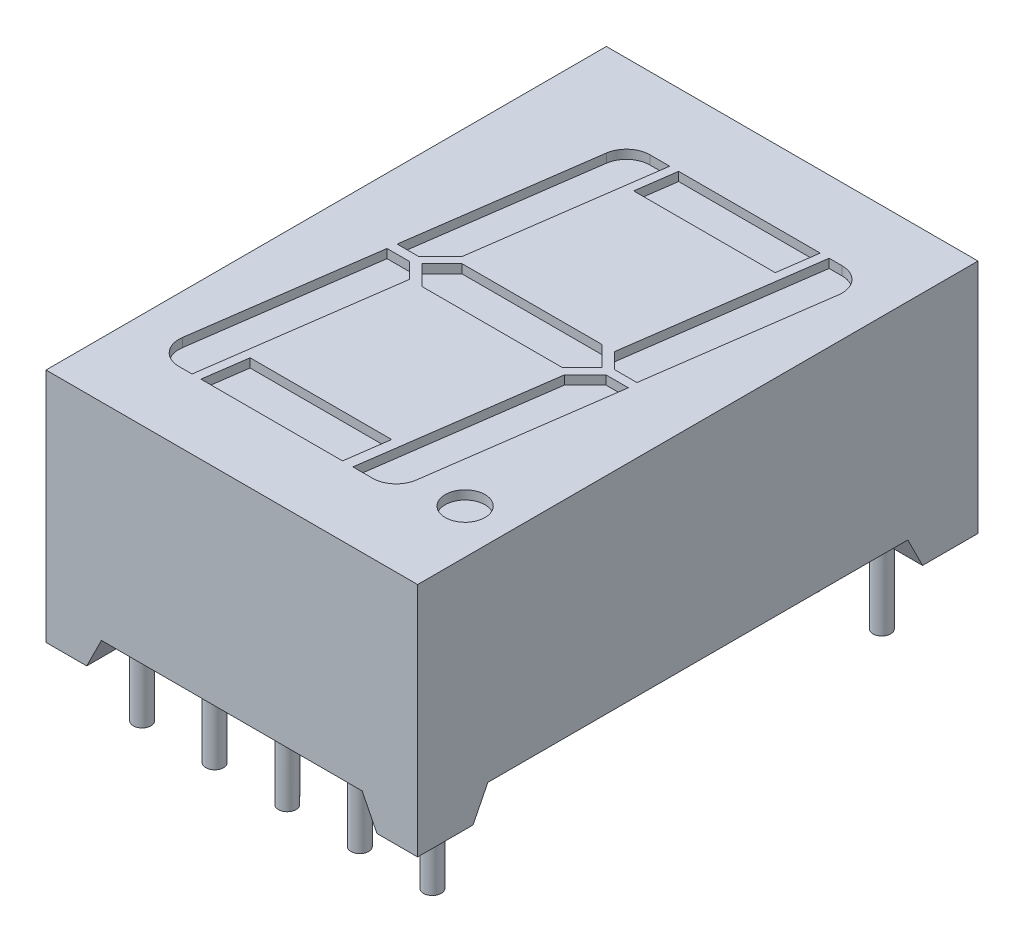
SolidWorks part; units mm, degrees
ref_plane "Front Plane" through (0, 0, 0) normal (0, 0, 1) x (1, 0, 0)
ref_plane "Top Plane" through (0, 0, 0) normal (0, 1, 0) x (1, 0, 0)
ref_plane "Right Plane" through (0, 0, 0) normal (1, 0, 0) x (0, 0, -1)
sketch "Sketch1" plane through (0, 0, 0) normal (0, 1, 0) x (1, 0, 0)
  line L0 (0, 5.3848) -> (0, -5.1523) construction
  line L1 (-6.3, 9.5) -> (6.3, 9.5)
  line L2 (-6.3, 9.5) -> (-6.3, -9.5)
  line L3 (-6.3, -9.5) -> (6.3, -9.5)
  line L4 (6.3, 9.5) -> (6.3, -9.5)
  line L5 (-4.2747, 0) -> (4.8609, 0) construction
  dimension "D1" = 19
  dimension "D2" = 12.6
extrude "Boss-Extrude1" add sketch "Sketch1" along normal blind 8
sketch "Sketch2" plane through (0, 0, 9.5) normal (0, 0, 1) x (1, 0, 0)
  line L0 (-4.92, 0) -> (4.92, 0)
  line L1 (-6.3, 0) -> (6.3, 0) construction
  line L2 (-4.92, 0) -> (-4.42, 1)
  line L3 (-4.42, 1) -> (4.42, 1)
  line L4 (4.42, 1) -> (4.92, 0)
  line L5 (0, 1) -> (0, 0.6203) construction
  line L6 (0, 0) -> (0, -0.1893) construction
  line L7 (0, -0.247) -> (0, 0.4162) construction
  dimension "D1" = 9.84
  dimension "D2" = 8.84
  dimension "D3" = 1
extrude "Cut-Extrude1" cut sketch "Sketch2" against normal through all
sketch "Sketch3" plane through (-6.3, 0, 0) normal (-1, 0, 0) x (0, 0, 1)
  line L0 (-7.62, 0) -> (7.62, 0)
  line L1 (-9.5, 0) -> (9.5, 0) construction
  line L2 (7.62, 0) -> (7.12, 1)
  line L3 (7.12, 1) -> (-7.12, 1)
  line L4 (-7.12, 1) -> (-7.62, 0)
  line L5 (0, 1) -> (0, 0.9495) construction
  line L6 (0, 0) -> (0, 0.4929) construction
  line L7 (0, 0) -> (0, 0.7864) construction
  dimension "D1" = 15.24
  dimension "D2" = 14.24
  dimension "D3" = 1
extrude "Cut-Extrude2" cut sketch "Sketch3" against normal through all
sketch "Sketch4" plane through (0, 8, 0) normal (0, 1, 0) x (1, 0, 0)
  line L0 (0, -8.8185) -> (0, 8.5813) construction
  line L1 (-5.8543, 0) -> (5.7357, 0) construction
  line L2 (0, 0) -> (1.1376, 8.0943) construction
  line L3 (0.9919, 7.0578) -> (0.804, 5.7209) construction
  line L4 (-1.4081, 7.0578) -> (3.3919, 7.0578)
  line L5 (-1.4081, 7.0578) -> (-1.596, 5.7209)
  line L6 (-1.596, 5.7209) -> (3.204, 5.7209)
  line L7 (3.3919, 7.0578) -> (3.204, 5.7209)
  line L8 (-3.1985, -5.6817) -> (1.6015, -5.6817)
  line L9 (-3.1985, -5.6817) -> (-3.4038, -7.1422)
  line L10 (-3.4038, -7.1422) -> (1.3962, -7.1422)
  line L11 (1.6015, -5.6817) -> (1.3962, -7.1422)
  line L12 (-0.7985, -5.6817) -> (-1.0038, -7.1422) construction
  line L13 (-3.0485, 0) -> (-2.3735, 0.675)
  line L14 (-2.3735, 0.675) -> (2.3735, 0.675)
  line L15 (2.3735, 0.675) -> (3.0485, 0)
  line L16 (3.0485, 0) -> (2.3735, -0.675)
  line L17 (2.3735, -0.675) -> (-2.3735, -0.675)
  line L18 (-2.3735, -0.675) -> (-3.0485, 0)
  line L19 (0, 0.675) -> (0, -0.675) construction
  line L20 (3.6949, 7.0578) -> (2.7978, 0.675)
  line L21 (2.7978, 0.675) -> (3.3228, 0.15)
  line L22 (3.3228, 0.15) -> (4.0873, 0.15)
  line L23 (4.0873, 0.15) -> (4.93, 6.1465)
  line L24 (4.1378, 7.0578) -> (3.6949, 7.0578)
  line L25 (3.3392, -0.15) -> (4.0942, -0.15)
  line L26 (4.0942, -0.15) -> (3.2083, -6.4535)
  line L27 (2.4161, -7.1422) -> (1.7483, -7.1422)
  line L28 (1.7483, -7.1422) -> (2.6315, -0.8577)
  line L29 (2.6315, -0.8577) -> (3.3392, -0.15)
  line L30 (-1.711, 7.0578) -> (-2.5771, 0.8958)
  line L31 (-2.5771, 0.8958) -> (-3.3228, 0.15)
  line L32 (-3.3228, 0.15) -> (-4.0451, 0.15)
  line L33 (-4.0451, 0.15) -> (-3.1711, 6.3691)
  line L34 (-2.3789, 7.0578) -> (-1.711, 7.0578)
  line L35 (-4.0873, -0.15) -> (-4.9419, -6.2309)
  line L36 (-4.1497, -7.1422) -> (-3.7067, -7.1422)
  line L37 (-3.7067, -7.1422) -> (-2.7978, -0.675)
  line L38 (-2.7978, -0.675) -> (-3.3228, -0.15)
  line L39 (-3.3228, -0.15) -> (-4.0873, -0.15)
  arc A0 (4.93, 6.1465) -> (4.1378, 7.0578) centre (4.1378, 6.2578) ccw
  arc A1 (-4.9419, -6.2309) -> (-4.1497, -7.1422) centre (-4.1497, -6.3422) ccw
  arc A2 (-2.3789, 7.0578) -> (-3.1711, 6.3691) centre (-2.3789, 6.2578) ccw
  arc A3 (3.2083, -6.4535) -> (2.4161, -7.1422) centre (2.4161, -6.3422) cw
  circle A4 centre (4.8, -6.39) radius 0.675
  dimension "D21" = 0.8
  dimension "D24" = 0.8
  dimension "D25" = 0.8
  dimension "D28" = 1.35
  dimension "D1" = 8
  dimension "D2" = 1.35
  dimension "D3" = 14.2
  dimension "D4" = 4.8
  dimension "D5" = 1.35
  dimension "D6" = 45
  dimension "D7" = 90
  dimension "D8" = 0.675
  dimension "D9" = 0.15
  dimension "D10" = 0.3
  dimension "D11" = 1.35
  dimension "D12" = 0.3
  dimension "D13" = 0.3
  dimension "D14" = 1.35
  dimension "D15" = 0.3
  dimension "D16" = 0.3
  dimension "D17" = 0.15
  dimension "D18" = 0.3
  dimension "D19" = 0.3
  dimension "D20" = 0.3
  dimension "D22" = 1.35
  dimension "D23" = 1.35
  dimension "D26" = 6.39
  dimension "D27" = 4.8
extrude "Cut-Extrude3" cut sketch "Sketch4" against normal blind 0.3
sketch "Sketch5" plane through (0, 1, 0) normal (0, -1, 0) x (1, 0, 0)
  line L0 (0, 2.9494) -> (0, 12.2906) construction
  line L1 (-2.3862, 0) -> (2.4158, 0) construction
  circle A0 centre (-4.92, 7.62) radius 0.3
  circle A1 centre (-2.46, 7.62) radius 0.3
  circle A2 centre (0, 7.62) radius 0.3
  circle A3 centre (2.46, 7.62) radius 0.3
  circle A4 centre (4.92, 7.62) radius 0.3
  circle A5 centre (-2.46, -7.62) radius 0.3
  circle A6 centre (0, -7.62) radius 0.3
  circle A7 centre (2.46, -7.62) radius 0.3
  circle A8 centre (4.92, -7.62) radius 0.3
  circle A9 centre (-4.92, -7.62) radius 0.3
  dimension "D1" = 0.6
  dimension "D2" = 5
  dimension "D3" = 2
extrude "Boss-Extrude2" add sketch "Sketch5" along normal blind 3.55
